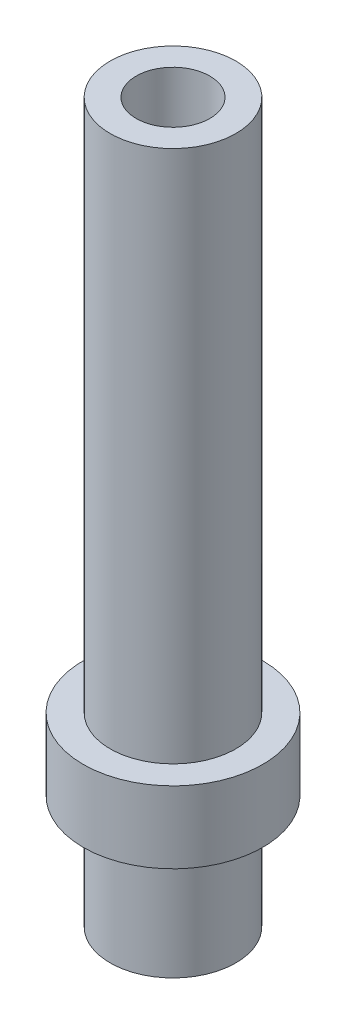
SolidWorks part; units mm, degrees
material "Cast Alloy Steel"
ref_plane "Front Plane" through (0, 0, 0) normal (0, 0, 1) x (1, 0, 0)
ref_plane "Top Plane" through (0, 0, 0) normal (0, 1, 0) x (1, 0, 0)
ref_plane "Right Plane" through (0, 0, 0) normal (1, 0, 0) x (0, 0, -1)
sketch "Sketch1" plane through (0, 0, 0) normal (1, 0, 0) x (0, 0, -1)
  line L0 (0, 0) -> (0, 62.475) construction
  line L1 (0, 27.5) -> (0, -27.5) construction
  line L2 (10.25, 0) -> (10.25, 200)
  line L3 (10.25, 200) -> (17.5, 200)
  line L4 (17.5, 200) -> (17.5, 51.6233)
  line L5 (17.5, 51.6233) -> (25, 51.6233)
  line L6 (25, 51.6233) -> (25, 31.6233)
  line L7 (25, 31.6233) -> (17.5, 31.6233)
  line L8 (17.5, 31.6233) -> (17.5, 0)
  line L9 (17.5, 0) -> (10.25, 0)
  dimension "D1" = 20.5
  dimension "D2" = 35
  dimension "D3" = 200
  dimension "D4" = 50
  dimension "D5" = 20
revolve "Revolve1" add sketch "Sketch1" angle 360 about L0
